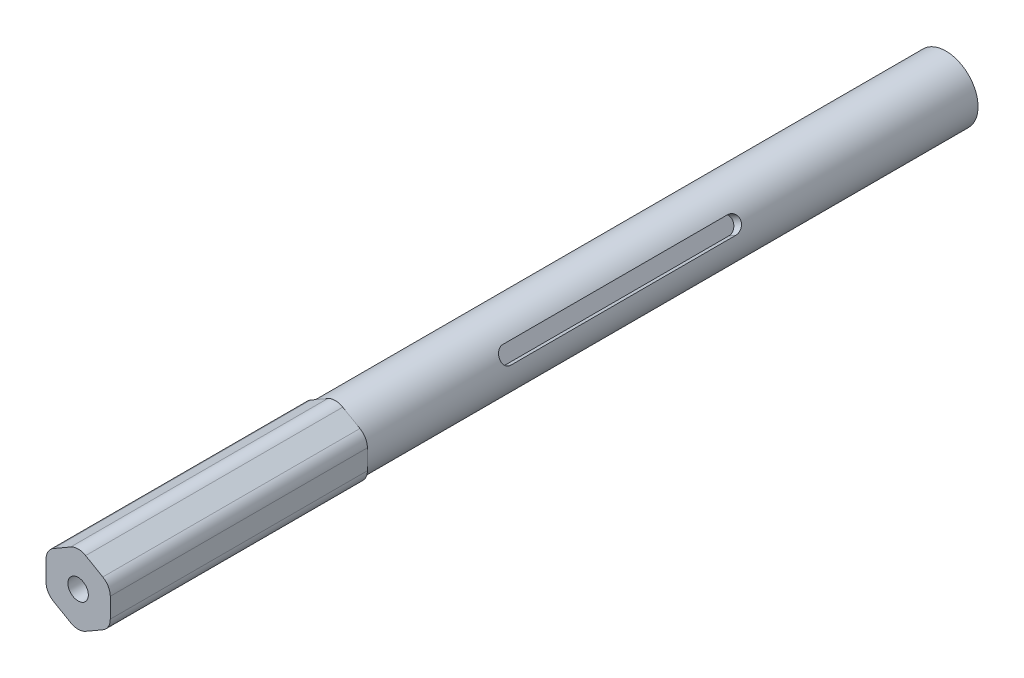
SolidWorks part; units mm, degrees
ref_plane "Front Plane" through (0, 0, 0) normal (0, 0, 1) x (1, 0, 0)
ref_plane "Top Plane" through (0, 0, 0) normal (0, 1, 0) x (1, 0, 0)
ref_plane "Right Plane" through (0, 0, 0) normal (1, 0, 0) x (0, 0, -1)
sketch "Sketch1" plane through (0, 0, 0) normal (0, 0, 1) x (1, 0, 0)
  line L1 (-6.35, 0) -> (6.35, 0) construction
  dimension "Width" = 12.7
sketch "Sketch2" plane through (0, 0, 0) normal (1, 0, 0) x (0, 0, -1)
  line L0 (152.4, 0) -> (-152.4, 0)
  point P4 (0, 0)
  dimension "Length" = 304.8
sketch "Sketch3" plane through (0, 0, 0) normal (0, 0, 1) x (1, 0, 0)
  line L1 (0, 7.3323) -> (-6.35, 3.6662)
  line L2 (-6.35, 3.6662) -> (-6.35, -3.6662)
  line L3 (-6.35, -3.6662) -> (0, -7.3323)
  line L4 (0, -7.3323) -> (6.35, -3.6662)
  line L5 (6.35, -3.6662) -> (6.35, 3.6662)
  line L6 (6.35, 3.6662) -> (0, 7.3323)
  circle A1 centre (0, 0) radius 6.35 construction
extrude "Boss-Extrude1" add sketch "Sketch3" along normal blind 171.45
fillet "Fillet1" radius 2.955 6 edges at (6.35, 3.6662, 85.725) (6.35, -3.6662, 85.725) (0, -7.3323, 85.725) (-6.35, -3.6662, 85.725) (-6.35, 3.6662, 85.725) (0, 7.3323, 85.725)
sketch "Sketch4" plane through (0, 0, 0) normal (0, 0, -1) x (-1, 0, 0)
  circle A0 centre (0, 0) radius 1
  dimension "D1" = 2
hole_wizard "Tap Drill for #10-32 Tap1" positions "Sketch6" profile "Sketch7" hole size "#10-32" standard "ANSI Inch"
sketch "Sketch6" plane through (0, 0, 0) normal (0, 0, -1) x (-1, 0, 0)
  point P0 (0, 0)
sketch "Sketch7" plane through (0, 0, 0) normal (1, 0, 0) x (0, 1, 0)
  line L0 (0, 0) -> (0, 13.9133)
  line L1 (0, 13.9133) -> (2.0193, 12.7)
  line L2 (2.0193, 12.7) -> (2.0193, 0)
  line L5 (2.0193, 0) -> (0, 0)
  line L10 (0, 13.9133) -> (-2.0193, 12.7) construction
  line L11 (0, -6.35) -> (0, 107.95) construction
  dimension "Hole Dia." = 4.0386
  dimension "Hole Depth" = 12.7
  dimension "Drill Angle" = 118
hole_wizard "Tap Drill for #10-32 Tap2" positions "Sketch8" profile "Sketch9" hole size "#10-32" standard "ANSI Inch"
sketch "Sketch8" plane through (0, 0, 171.45) normal (0, 0, 1) x (1, 0, 0)
  point P0 (0, 0)
sketch "Sketch9" plane through (0, 0, 171.45) normal (1, 0, 0) x (0, -1, 0)
  line L0 (0, 0) -> (0, 13.9133)
  line L1 (0, 13.9133) -> (2.0193, 12.7)
  line L2 (2.0193, 12.7) -> (2.0193, 0)
  line L5 (2.0193, 0) -> (0, 0)
  line L10 (0, 13.9133) -> (-2.0193, 12.7) construction
  line L11 (0, -6.35) -> (0, 107.95) construction
  dimension "Hole Dia." = 4.0386
  dimension "Hole Depth" = 12.7
  dimension "Drill Angle" = 118
sketch "Sketch11" plane through (3.175, 5.4993, 0) normal (0.5, 0.866, 0) x (0.866, -0.5, 0)
  line L0 (0, 0) -> (0, -31.75) construction
  line L1 (-1.5875, -31.75) -> (1.5875, -31.75)
  line L2 (-1.5875, -31.75) -> (-1.5875, -69.85)
  line L3 (-1.5875, -69.85) -> (1.5875, -69.85)
  line L4 (1.5875, -31.75) -> (1.5875, -69.85)
  line L5 (-1.5875, -31.75) -> (1.5875, -69.85) construction
  line L6 (-1.5875, -69.85) -> (1.5875, -31.75) construction
  arc A0 (-1.5875, -31.75) -> (1.5875, -31.75) centre (0, -31.75) cw
  arc A1 (-1.5875, -69.85) -> (1.5875, -69.85) centre (0, -69.85) ccw
  point P4 (0, -50.8)
  dimension "D1" = 31.75
  dimension "D2" = 38.1
  dimension "D3" = 3.175
extrude "Cut-Extrude1" [suppressed] cut sketch "Sketch11" against normal blind 1.5875 contours L4 L1 L2 L3 | A0 L1 | L3 A1
sketch "Sketch12" plane through (0, 0, 0) normal (0, 0, -1) x (-1, 0, 0)
  circle A0 centre (0, 0) radius 6.35
  dimension "D1" = 12.7
extrude "Cut-Extrude2" cut sketch "Sketch12" against normal blind 120.65 flip side to cut
ref_plane "Plane1" through (5.6112, 3.2397, 0) normal (-0.866, -0.5, 0) x (0, 0, 1)
sketch "Sketch13" plane through (5.6112, 3.2397, 0) normal (-0.866, -0.5, 0) x (0, 0, 1)
  line L0 (47.625, 0) -> (0, 0) construction
  line L1 (92.075, 1.5875) -> (47.625, 1.5875)
  line L2 (92.075, 1.5875) -> (92.075, -1.5875) construction
  line L3 (92.075, -1.5875) -> (47.625, -1.5875)
  line L4 (47.625, 1.5875) -> (47.625, -1.5875) construction
  line L5 (92.075, 1.5875) -> (47.625, -1.5875) construction
  line L6 (92.075, -1.5875) -> (47.625, 1.5875) construction
  arc A0 (47.625, -1.5875) -> (47.625, 1.5875) centre (47.625, 0) cw
  arc A1 (92.075, 1.5875) -> (92.075, -1.5875) centre (92.075, 0) cw
  point P4 (69.85, 0)
  dimension "D1" = 47.625
  dimension "D2" = 44.45
  dimension "D3" = 3.175
extrude "Cut-Extrude3" cut sketch "Sketch13" along normal blind 1.9177 contours L3 A0 L1 A1
